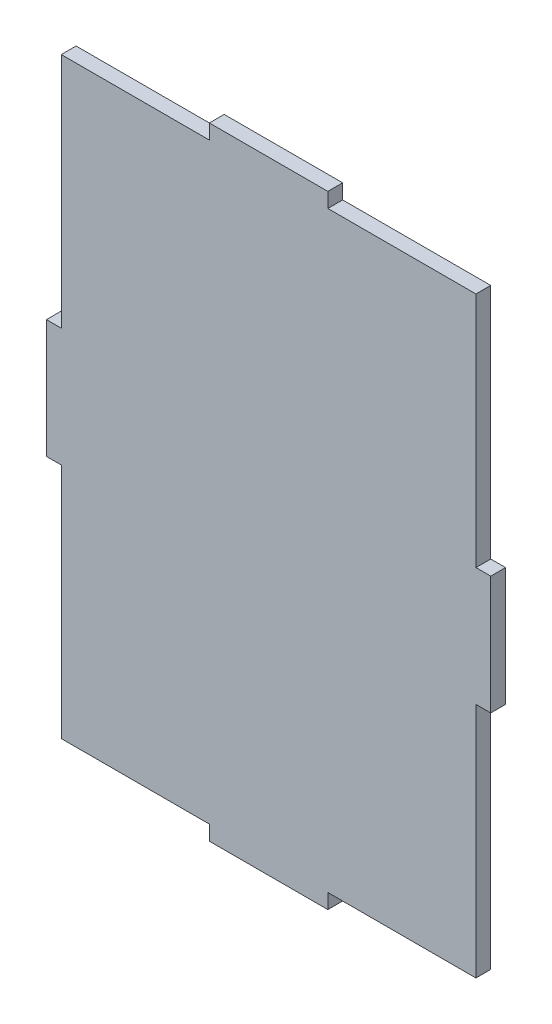
SolidWorks part; units mm, degrees
ref_plane "Alzado" through (0, 0, 0) normal (0, 0, 1) x (1, 0, 0)
ref_plane "Planta" through (0, 0, 0) normal (0, 1, 0) x (1, 0, 0)
ref_plane "Vista lateral" through (0, 0, 0) normal (1, 0, 0) x (0, 0, -1)
sketch "Croquis1" plane through (0, 0, 0) normal (0, 0, 1) x (1, 0, 0)
  line L0 (-20, 100) -> (-70, 100)
  line L3 (70, 100) -> (20, 100)
  line L4 (-70, -100) -> (-70, -20)
  line L5 (70, -100) -> (-70, 100) construction
  line L6 (70, 100) -> (-70, -100) construction
  line L8 (-20, 100) -> (-20, 105)
  line L9 (-20, 105) -> (20, 105)
  line L10 (20, 100) -> (20, 105)
  line L11 (75, 0) -> (-75, 0) construction
  line L12 (20, -100) -> (20, -105)
  line L13 (-20, -105) -> (20, -105)
  line L14 (-20, -100) -> (-20, -105)
  line L15 (70, -100) -> (20, -100)
  line L16 (-20, -100) -> (-70, -100)
  line L17 (-70, 20) -> (-70, 100)
  line L18 (-70, -20) -> (-75, -20)
  line L20 (-70, 20) -> (-75, 20)
  line L21 (-75, -20) -> (-75, 20)
  line L22 (0, 0) -> (0, 55.2944) construction
  line L23 (75, -20) -> (75, 20)
  line L24 (70, 20) -> (75, 20)
  line L25 (70, -20) -> (75, -20)
  line L26 (70, 20) -> (70, 100)
  line L27 (70, -100) -> (70, -20)
  point P0 (0, 0)
  point P11 (0, 105)
  point P21 (-75, 0)
  dimension "D1" = 140
  dimension "D2" = 200
  dimension "D3" = 5
  dimension "D4" = 40
  dimension "D5" = 5
  dimension "D6" = 40
extrude "Saliente-Extruir1" add sketch "Croquis1" along normal blind 5
